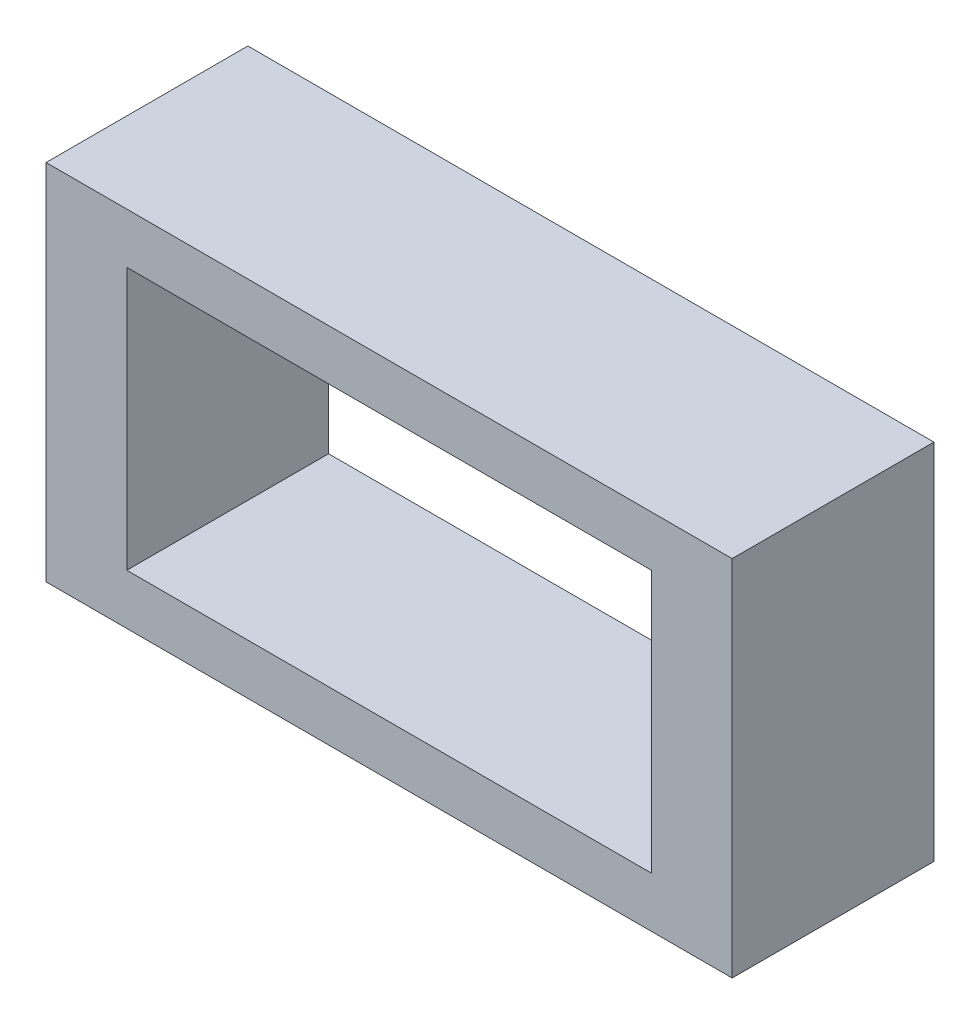
SolidWorks part; units mm, degrees
ref_plane "Plan de face" through (0, 0, 0) normal (0, 0, 1) x (1, 0, 0)
ref_plane "Plan de dessus" through (0, 0, 0) normal (0, 1, 0) x (1, 0, 0)
ref_plane "Plan de droite" through (0, 0, 0) normal (1, 0, 0) x (0, 0, -1)
sketch "Esquisse1" plane through (0, 0, 0) normal (0, 0, 1) x (1, 0, 0)
  line L1 (-8.5, 4.5) -> (8.5, 4.5)
  line L2 (-8.5, 4.5) -> (-8.5, -4.5)
  line L3 (-8.5, -4.5) -> (8.5, -4.5)
  line L4 (8.5, 4.5) -> (8.5, -4.5)
  line L5 (-8.5, 4.5) -> (8.5, -4.5) construction
  line L6 (-8.5, -4.5) -> (8.5, 4.5) construction
  point P0 (0, 0)
  dimension "D1" = 17
  dimension "D2" = 9
extrude "Boss.-Extru.1" add sketch "Esquisse1" along normal blind 5
sketch "Esquisse2" plane through (0, 0, 5) normal (0, 0, 1) x (1, 0, 0)
  line L1 (-6.5, 3.25) -> (6.5, 3.25)
  line L2 (-6.5, 3.25) -> (-6.5, -3.25)
  line L3 (-6.5, -3.25) -> (6.5, -3.25)
  line L4 (6.5, 3.25) -> (6.5, -3.25)
  line L5 (-6.5, 3.25) -> (6.5, -3.25) construction
  line L6 (-6.5, -3.25) -> (6.5, 3.25) construction
  point P0 (0, 0)
  dimension "D1" = 13
  dimension "D2" = 6.5
extrude "Enlèv. mat.-Extru.1" cut sketch "Esquisse2" against normal up to surface (5 mm away) contours L1 L4 L3 L2 up to face at (0, 0, 0)
